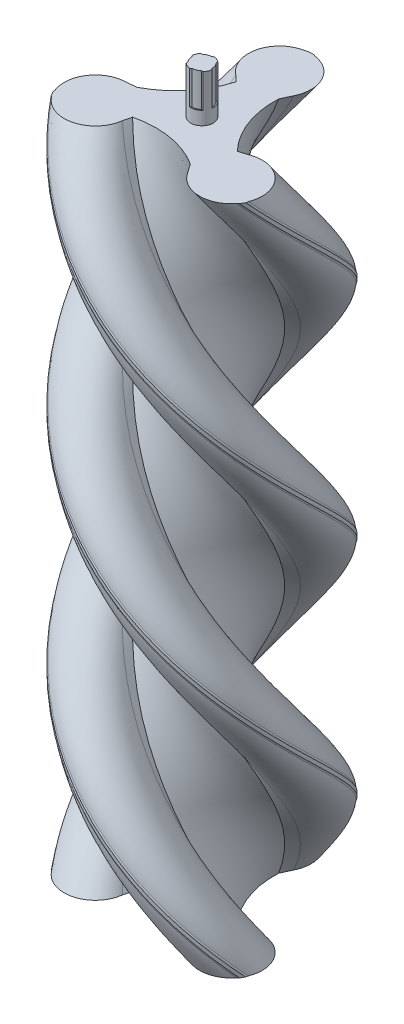
SolidWorks part; units mm, degrees
ref_plane "Front Plane" through (0, 0, 0) normal (0, 0, 1) x (1, 0, 0)
ref_plane "Top Plane" through (0, 0, 0) normal (0, 1, 0) x (1, 0, 0)
ref_plane "Right Plane" through (0, 0, 0) normal (1, 0, 0) x (0, 0, -1)
sketch "Sketch1" plane through (0, 0, 0) normal (0, 1, 0) x (1, 0, 0)
  line L0 (-5.6637, 20.9393) -> (0, 0)
  line L1 (0, 0) -> (21.4822, -5.7017)
  line L2 (10.2665, 24.0669) -> (12.382, 28.5973)
  line L3 (-1.1287, 49.0807) -> (0.8713, 49.0807)
  line L4 (-8.5567, 23.7017) -> (-5.6637, 20.9393)
  line L5 (-1.1287, 49.0807) -> (-2.1287, 48.7371)
  line L6 (0.8713, 49.0807) -> (1.8713, 48.7371)
  arc A0 (12.382, 28.5973) -> (1.8713, 48.7371) centre (-0.1287, 34.8807) ccw
  arc A1 (-2.1287, 48.7371) -> (-8.5567, 23.7017) centre (-0.1287, 34.8807) ccw
  arc A2 (10.2665, 24.0669) -> (21.4822, -5.7017) centre (50.2192, 22.1224) ccw
  point P0 (12.7878, 8.0197)
  dimension "D5" = 5
  dimension "D2" = 4
  dimension "D3" = 21.4822
  dimension "D4" = 40
  dimension "D6" = 21.6917
  dimension "D7" = 120
  dimension "D11" = 25.8952
  dimension "D12" = 34.299
  dimension "D13" = 14.2
  dimension "D14" = 2
  dimension "D16" = 1
  dimension "D8" = 28
  dimension "D9" = 15.9303
  dimension "D10" = 148.814
  dimension "D15" = 26.861
  dimension "D17" = 1
  dimension "D18" = 1
sketch "Sketch2" plane through (0, 0, 0) normal (0, 1, 0) x (1, 0, 0)
  circle A0 centre (0, 0) radius 49.6712
curve "Helix/Spiral1" pitch 300 height 300 turns 1
sweep "Sweep1" add profiles "Sketch1" path "Helix/Spiral1"
pattern_circular "CirPattern1" count 3 over 360 about axis through (0, 150, 0) along (0, 1, 0) of "Sweep1"
sketch "Sketch4" plane through (0, 0, 0) normal (0, -1, 0) x (-1, 0, 0)
  circle A0 centre (0, 0) radius 5
  dimension "D1" = 10
extrude "Boss-Extrude1" add sketch "Sketch4" along normal blind 20 and the other way blind 321
sketch "Sketch5" plane through (0, 321, 0) normal (0, 1, 0) x (1, 0, 0)
  line L0 (-3.7988, 3.2824) -> (3.7988, -3.2824)
  line L1 (0.5424, 4.9705) -> (-4.9705, 0.5424)
  line L2 (-4.9705, 0.5424) -> (-0.5424, -4.9705)
  line L3 (-0.5424, -4.9705) -> (4.9705, -0.5424)
  line L4 (4.9705, -0.5424) -> (0.5424, 4.9705)
  line L5 (-3.7988, 3.2824) -> (-3.2824, -3.7988)
  line L6 (-3.2824, -3.7988) -> (3.7988, -3.2824)
  line L7 (3.7988, -3.2824) -> (3.2824, 3.7988)
  line L8 (3.2824, 3.7988) -> (-3.7988, 3.2824)
  circle A0 centre (0, 0) radius 3.5355 construction
  circle A1 centre (0, 0) radius 3.55 construction
  circle A2 centre (0, 0) radius 4.5
  circle A3 centre (0, 0) radius 5
  circle M2 centre (0, 0) radius 5
  dimension "D3" = 9
  dimension "D4" = 10
  dimension "D1" = 2.74
  dimension "D2" = 7.1
  dimension "D5" = 2.98
extrude "Cut-Extrude1" cut sketch "Sketch5" against normal blind 15 contours A2 L1 L8 M2 | A2 L4 L7 M2 | A2 L3 L6 M2 | A2 L2 L5 M2
